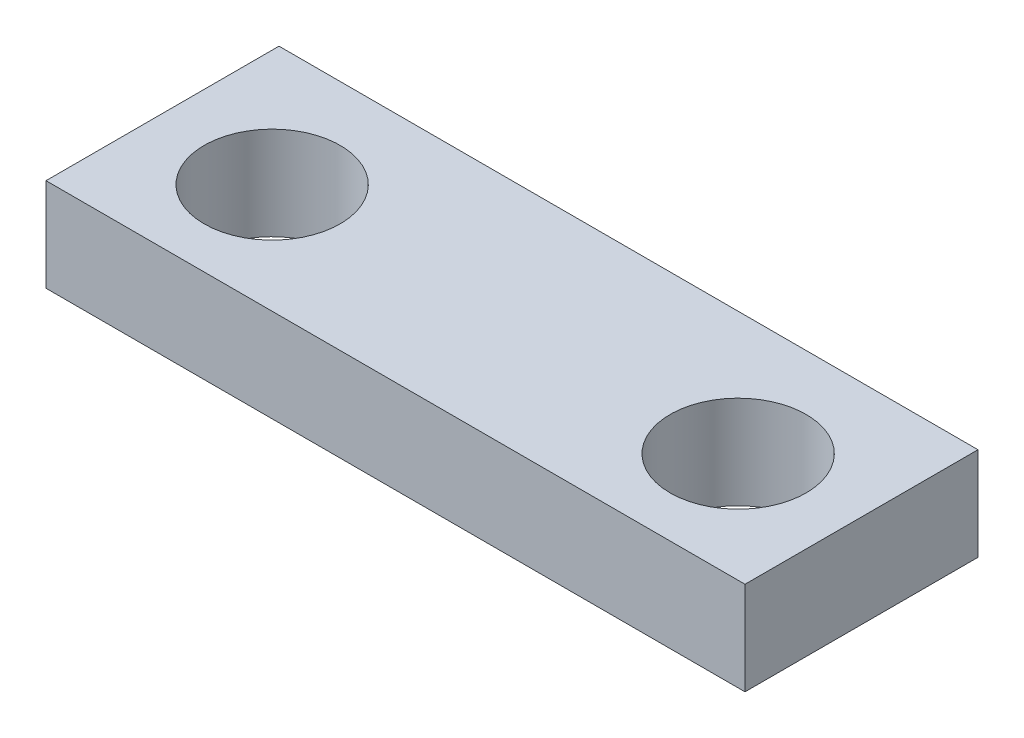
SolidWorks part; units mm, degrees
ref_plane "Front Plane" through (0, 0, 0) normal (0, 0, 1) x (1, 0, 0)
ref_plane "Top Plane" through (0, 0, 0) normal (0, 1, 0) x (1, 0, 0)
ref_plane "Right Plane" through (0, 0, 0) normal (1, 0, 0) x (0, 0, -1)
sketch "Sketch3" plane through (0, 0, 0) normal (0, 1, 0) x (1, 0, 0)
  line L0 (-7.0588, -0.8824) -> (7.9412, -0.8824) construction
  line L1 (-7.0588, 1.7647) -> (7.9412, 1.7647)
  line L2 (-7.0588, 1.7647) -> (-7.0588, -3.2353)
  line L3 (-7.0588, -3.2353) -> (7.9412, -3.2353)
  line L4 (7.9412, 1.7647) -> (7.9412, -3.2353)
  line L5 (0.4412, -0.8824) -> (0.4412, 1.7647) construction
  line L6 (0.4412, -0.8824) -> (3.9817, -0.8824)
  circle A0 centre (5.4412, -0.8824) radius 1.4595
  circle A1 centre (-4.5588, -0.8824) radius 1.4595
  dimension "D1" = 15
  dimension "D2" = 5
  dimension "D3" = 5
extrude "Boss-Extrude1" add sketch "Sketch3" against normal blind 2
